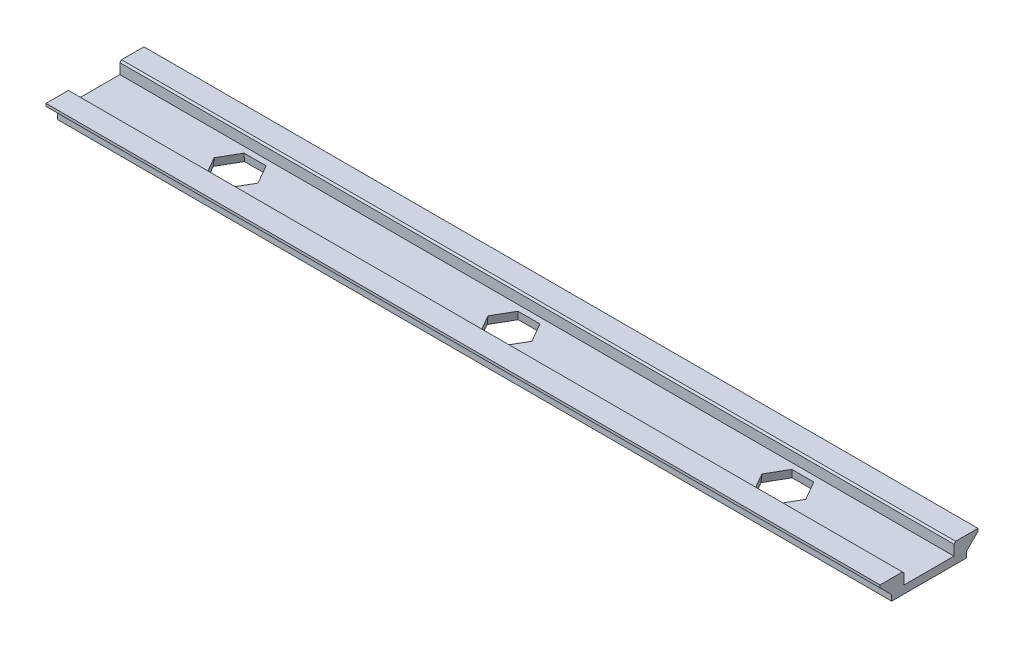
SolidWorks part; units mm, degrees
ref_plane "Front Plane" through (0, 0, 0) normal (0, 0, 1) x (1, 0, 0)
ref_plane "Top Plane" through (0, 0, 0) normal (0, 1, 0) x (1, 0, 0)
ref_plane "Right Plane" through (0, 0, 0) normal (1, 0, 0) x (0, 0, -1)
sketch "Retainer Profile" plane through (0, 0, 0) normal (1, 0, 0) x (0, 0, -1)
  line L1 (-4.7, 2.7923) -> (-4.7, 2.1923) construction
  line L2 (-6.1, 4.1923) -> (-4.7, 2.7923) construction
  line L8 (-6.1, 4.7923) -> (-6.1, 4.1923) construction
  line L9 (-5.1, 4.7923) -> (-6.1, 4.7923) construction
  line L10 (-4.7, 2.7923) -> (-4.7, 2.1923) construction
  line L11 (-6.1, 4.1923) -> (-4.7, 2.7923) construction
  line L23 (0, -28.6883) -> (0, 28.6883) construction
  line L24 (0, -28.6883) -> (0, 28.6883) construction
  line L27 (-6.1, 4.7923) -> (-6.1, 4.1923) construction
  line L28 (-5.1, 4.7923) -> (-6.1, 4.7923) construction
  line L31 (-5.1, 4.5923) -> (-5.9, 4.5923)
  line L32 (-5.9, 4.5923) -> (-5.9, 4.2751)
  line L33 (-5.9, 4.2751) -> (-4.5, 2.8751)
  line L34 (-4.5, 2.8751) -> (-4.5, 2.1923)
  line L35 (-5.1, 4.5923) -> (-3, 4.5923)
  line L36 (-3, 4.5923) -> (-3, 3.1423)
  line L37 (-3, 3.1423) -> (3, 3.1423)
  line L38 (-4.5, 2.1923) -> (4.5, 2.1923)
  line L39 (3, 4.5923) -> (3, 3.1423)
  line L40 (5.1, 4.5923) -> (3, 4.5923)
  line L41 (4.5, 2.8751) -> (4.5, 2.1923)
  line L42 (5.9, 4.2751) -> (4.5, 2.8751)
  line L43 (5.9, 4.5923) -> (5.9, 4.2751)
  line L44 (5.1, 4.5923) -> (5.9, 4.5923)
  point P15 (0, 2.1923)
  point P16 (0, 3.1423)
  dimension "D3" = 3
  dimension "D1" = 0.2
  dimension "D2" = 1.45
extrude "Boss-Extrude1" add sketch "Retainer Profile" along normal mid plane 100.5
sketch "Sketch3" plane through (0, 4.5923, 0) normal (0, 1, 0) x (1, 0, 0)
  line L0 (50.25, -5.1) -> (50.25, 5.1) construction
  line L1 (35.25, 0) -> (34, 2.1651)
  line L2 (34, 2.1651) -> (31.5, 2.1651)
  line L3 (31.5, 2.1651) -> (30.25, 0)
  line L4 (30.25, 0) -> (31.5, -2.1651)
  line L5 (31.5, -2.1651) -> (34, -2.1651)
  line L6 (34, -2.1651) -> (35.25, 0)
  line L7 (2.25, 0) -> (1, 2.1651)
  line L8 (1, 2.1651) -> (-1.5, 2.1651)
  line L9 (-1.5, 2.1651) -> (-2.75, 0)
  line L10 (-2.75, 0) -> (-1.5, -2.1651)
  line L11 (-1.5, -2.1651) -> (1, -2.1651)
  line L12 (1, -2.1651) -> (2.25, 0)
  line L13 (-30.75, 0) -> (-32, 2.1651)
  line L14 (-32, 2.1651) -> (-34.5, 2.1651)
  line L15 (-34.5, 2.1651) -> (-35.75, 0)
  line L16 (-35.75, 0) -> (-34.5, -2.1651)
  line L17 (-34.5, -2.1651) -> (-32, -2.1651)
  line L18 (-32, -2.1651) -> (-30.75, 0)
  circle A0 centre (32.75, 0) radius 2.1651 construction
  circle A1 centre (-0.25, 0) radius 2.1651 construction
  circle A2 centre (-33.25, 0) radius 2.1651 construction
  dimension "D1" = 5
  dimension "D2" = 15
  dimension "D3" = 3
extrude "Cut-Extrude2" cut sketch "Sketch3" against normal through all draft 5 draft outward yes
chamfer "Chamfer1" distance 0.2 angle 45 2 edges at (0, 4.5923, 3) (0, 4.5923, -3)
